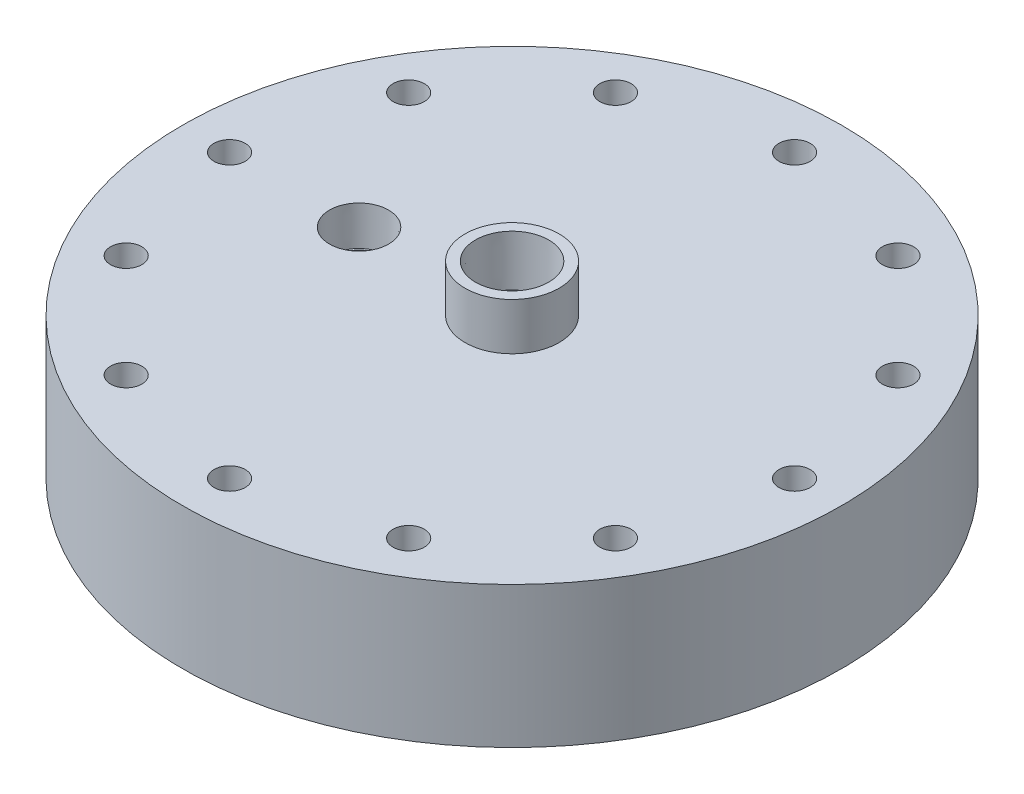
SolidWorks part; units mm, degrees
ref_plane "Front Plane" through (0, 0, 0) normal (0, 0, 1) x (1, 0, 0)
ref_plane "Top Plane" through (0, 0, 0) normal (0, 1, 0) x (1, 0, 0)
ref_plane "Right Plane" through (0, 0, 0) normal (1, 0, 0) x (0, 0, -1)
sketch "Sketch1" plane through (0, 0, 0) normal (0, 0, 1) x (1, 0, 0)
  line L0 (0, 0) -> (0, 51.199) construction
  line L1 (-55.9435, 0) -> (-88.9, 0)
  line L2 (-88.9, 0) -> (-88.9, 38.1)
  line L3 (-88.9, 38.1) -> (-12.7, 38.1)
  line L4 (-12.7, 38.1) -> (-12.7, 50.8)
  line L5 (-12.7, 50.8) -> (0, 50.8)
  line L6 (0, 50.8) -> (0, 31.75)
  line L8 (-25.4, 31.75) -> (0, 31.75)
  line L12 (-25.4, 31.75) -> (-25.4, 19.05)
  line L13 (-25.4, 19.05) -> (-31.75, 19.05)
  line L14 (-31.75, 19.05) -> (-31.75, 12.7)
  line L15 (-31.75, 12.7) -> (-50.8, 12.7)
  line L16 (-50.8, 12.7) -> (-50.8, 0)
  line L17 (-50.8, 0) -> (-52.3875, 0)
  line L18 (-52.3875, 0) -> (-52.3875, 2.54)
  line L19 (-52.3875, 2.54) -> (-55.9435, 2.54)
  line L20 (-55.9435, 2.54) -> (-55.9435, 0)
  dimension "D1" = 6.35
  dimension "D2" = 25.4
  dimension "D3" = 12.7
  dimension "D4" = 12.7
  dimension "D5" = 88.9
  dimension "D6" = 12.7
  dimension "D8" = 6.35
  dimension "D9" = 12.7
  dimension "D10" = 38.1
  dimension "D11" = 6.35
  dimension "D12" = 50.8
  dimension "D13" = 3.556
  dimension "D14" = 2.54
  dimension "D15" = 1.5875
revolve "Revolve1" add sketch "Sketch1" angle 360 about L0
hole_wizard "1/2 NPT Tapped Hole1" positions "Sketch7" profile "Sketch8" size "1/2" standard "ANSI Inch" end condition through all
sketch "Sketch7" plane through (0, 50.8, 0) normal (0, 1, 0) x (1, 0, 0)
  point P0 (0, 0)
sketch "Sketch8" plane through (0, 50.8, 0) normal (1, 0, 0) x (0, 0, 1)
  line L0 (0, 0) -> (0, 50.8)
  line L1 (0, 50.8) -> (8.9281, 50.8)
  line L2 (-9.4797, 13.462) -> (-9.8828, 0) construction
  line L3 (8.9281, 50.8) -> (8.9281, 13.462)
  line L4 (8.9281, 13.462) -> (9.4797, 13.462)
  line L5 (9.4797, 13.462) -> (9.8828, 0)
  line L7 (9.8828, 0) -> (0, 0)
  line L8 (0, -6.35) -> (0, 107.95) construction
  line L11 (-8.9281, 13.462) -> (-9.4797, 13.462) construction
  dimension "Thru Tap Drill Dia." = 17.8562
  dimension "Thru Tap Drill Depth" = 50.8
  dimension "Thread Dia." = 19.7656
  dimension "Thread Angle" = 3.43
  dimension "Thread Depth" = 13.462
cosmetic thread "Hole Thread2" parameters "D1"=13.462, "D2"=21.3288
hole_wizard "3/8 NPT Tapped Hole1" positions "Sketch2" profile "Sketch3" size "3/8" standard "ANSI Inch"
sketch "Sketch2" plane through (0, 38.1, 0) normal (0, 1, 0) x (1, 0, 0)
  point P0 (-41.275, 0)
  dimension "D1" = 41.275
sketch "Sketch3" plane through (-41.275, 38.1, 0) normal (1, 0, 0) x (0, 0, 1)
  line L0 (0, 0) -> (0, 29.6886)
  line L1 (7.1374, 25.4) -> (0, 29.6886)
  line L2 (-7.1374, 25.4) -> (0, 29.6886) construction
  line L3 (7.1374, 25.4) -> (7.1374, 10.414)
  line L4 (7.1374, 10.414) -> (7.6537, 10.414)
  line L5 (7.6537, 10.414) -> (7.9655, 0)
  line L6 (-7.6537, 10.414) -> (-7.9655, 0) construction
  line L7 (7.9655, 0) -> (0, 0)
  line L8 (0, -6.35) -> (0, 107.95) construction
  line L11 (-7.1374, 10.414) -> (-7.6537, 10.414) construction
  dimension "Tap Drill Dia." = 14.2748
  dimension "Tap Drill Depth" = 25.4
  dimension "Thread Dia." = 15.9311
  dimension "Thread Angle" = 3.43
  dimension "Thread Depth" = 10.414
  dimension "Drill Angle" = 118
cosmetic thread "Hole Thread1" parameters "D1"=10.414, "D2"=17.1495
hole_wizard "5/16 Clearance Hole1" positions "Sketch4" profile "Sketch6" hole size "5/16" standard "ANSI Inch" end condition through all
sketch "Sketch4" plane through (0, 38.1, 0) normal (0, 1, 0) x (1, 0, 0)
  point P0 (-76.2, 0)
  dimension "D1" = 76.2
sketch "Sketch6" plane through (-76.2, 38.1, 0) normal (1, 0, 0) x (0, 0, 1)
  line L0 (0, 0) -> (0, 38.1)
  line L1 (0, 38.1) -> (4.2164, 38.1)
  line L2 (4.2164, 38.1) -> (4.2164, 0)
  line L5 (4.2164, 0) -> (0, 0)
  line L11 (0, -6.35) -> (0, 107.95) construction
  dimension "Thru Hole Dia." = 8.4328
  dimension "Thru Hole Depth" = 38.1
pattern_circular "CirPattern1" count 12 over 360 about axis through (0, 0, 0) along (0, 1, 0) of "5/16 Clearance Hole1"
